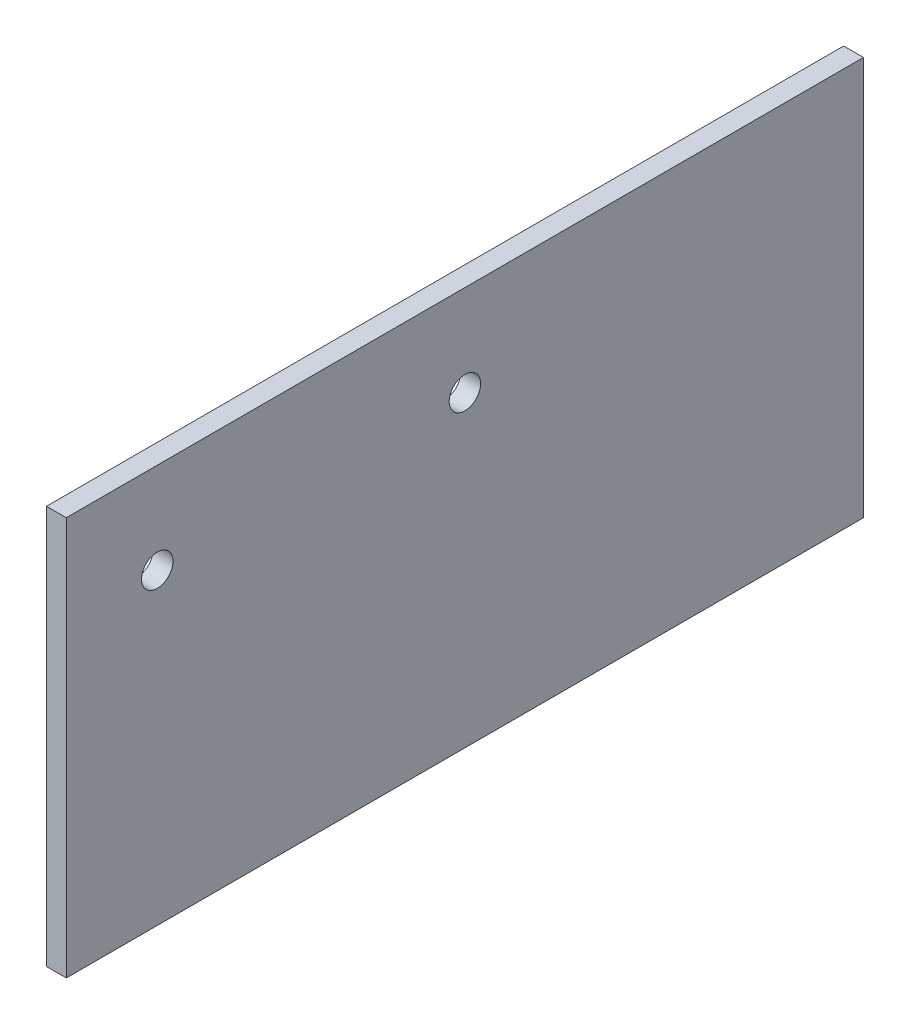
SolidWorks part; units mm, degrees
material "Black Acrylic"
ref_plane "Front Plane" through (0, 0, 0) normal (0, 0, 1) x (1, 0, 0)
ref_plane "Top Plane" through (0, 0, 0) normal (0, 1, 0) x (1, 0, 0)
ref_plane "Right Plane" through (0, 0, 0) normal (1, 0, 0) x (0, 0, -1)
sketch "Sketch1" plane through (0, 0, 0) normal (1, 0, 0) x (0, 0, -1)
  line L1 (-90.5, 90.5) -> (90.5, 90.5)
  line L2 (-90.5, 90.5) -> (-90.5, 0)
  line L3 (-90.5, 0) -> (90.5, 0)
  line L4 (90.5, -90.5) -> (-90.5, 90.5) construction
  line L5 (-90.5, -90.5) -> (90.5, 90.5) construction
  line L6 (90.5, -90.5) -> (90.5, 90.5) construction
  line L7 (90.5, 90.5) -> (90.5, 0)
  point P4 (0, 0)
  dimension "D1" = 181
  dimension "D2" = 181
extrude "Boss-Extrude1" add sketch "Sketch1" along normal mid plane 4.5
extrude "Cut-Extrude1" cut sketch "Sketch2" against normal through all both and the other way through all
sketch "Sketch2" plane through (88.25, 0, 0) normal (1, 0, 0) x (0, 0, -1)
  line L0 (0, -69.85) -> (0, 69.85) construction
  line L1 (0, 69.85) -> (-69.85, 69.85) construction
  line L2 (69.85, -69.85) -> (0, -69.85) construction
  circle A0 centre (0, -69.85) radius 3.5687
  circle A1 centre (-69.85, 69.85) radius 3.5687
  circle A2 centre (69.85, -69.85) radius 3.5687
  circle A3 centre (0, 69.85) radius 3.5687
